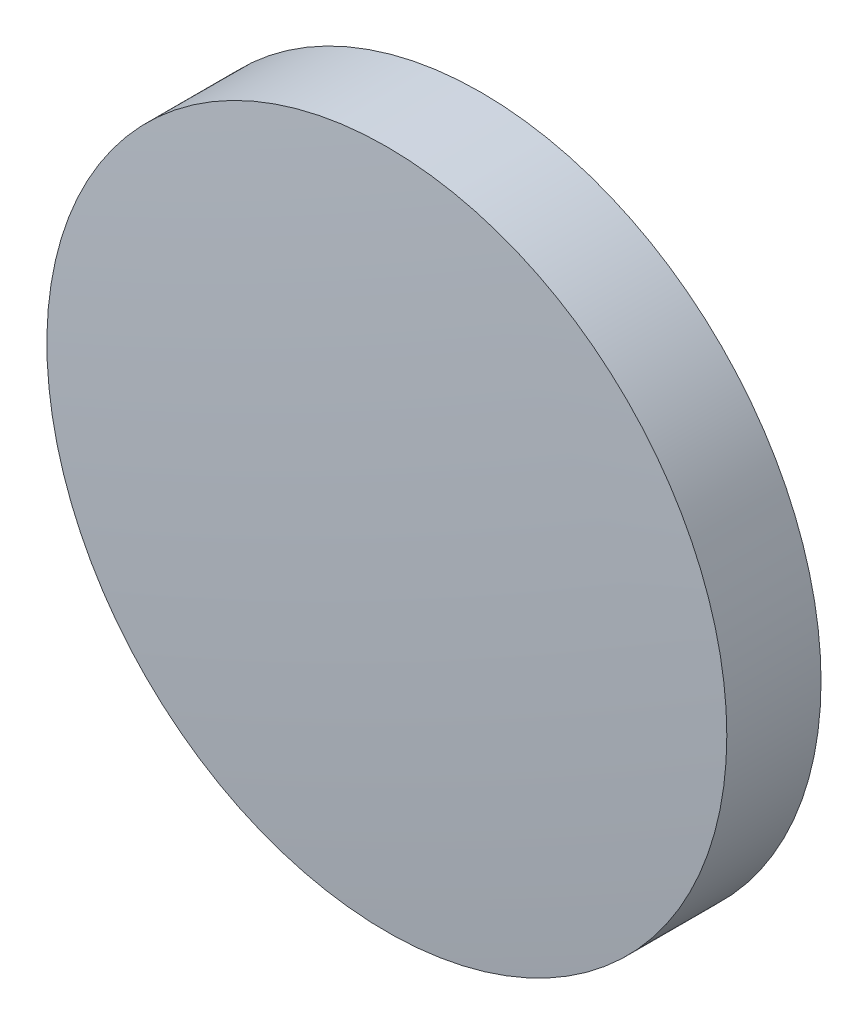
SolidWorks part; units mm, degrees
material "Glass"
ref_plane "Front Plane" through (0, 0, 0) normal (0, 0, 1) x (1, 0, 0)
ref_plane "Top Plane" through (0, 0, 0) normal (0, 1, 0) x (1, 0, 0)
ref_plane "Right Plane" through (0, 0, 0) normal (1, 0, 0) x (0, 0, -1)
sketch "Sketch2" plane through (0, 0, 0) normal (1, 0, 0) x (0, 0, -1)
  line L0 (-1.1, 0) -> (1.1, 0)
  line L1 (-0.8799, 6.35) -> (0.8799, 6.35)
  arc A0 (1.1, 0) -> (0.8799, 6.35) centre (-90.6, 0) ccw
  arc A1 (-1.1, 0) -> (-0.8799, 6.35) centre (90.6, 0) cw
  dimension "R2" = 91.7
  dimension "R1" = 91.7
  dimension "D1" = 6.35
  dimension "CT" = 2.2
revolve "Revolve1" add sketch "Sketch2" angle 360 about L0
